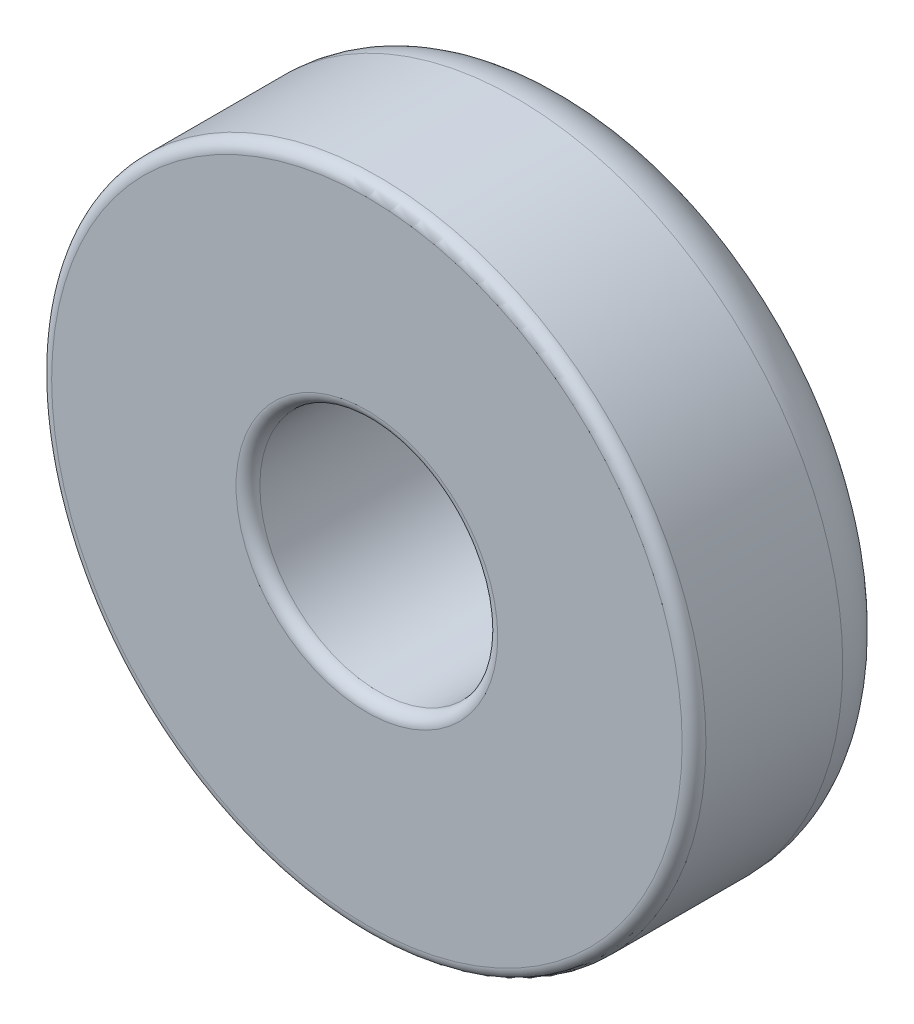
SolidWorks part; units mm, degrees
material "iglidur® X"
ref_plane "Front Plane" through (0, 0, 0) normal (0, 0, 1) x (1, 0, 0)
ref_plane "Top Plane" through (0, 0, 0) normal (0, 1, 0) x (1, 0, 0)
ref_plane "Right Plane" through (0, 0, 0) normal (1, 0, 0) x (0, 0, -1)
sketch "Sketch1" plane through (0, 0, 0) normal (0, 0, 1) x (1, 0, 0)
  circle A0 centre (0, 0) radius 1
  dimension "D1" = 2
extrude "Extrude-Thin1" add sketch "Sketch1" along normal blind 1.75 thin
fillet "Fillet1" radius 0.5 1 edges at (2.75, 0, 0)
fillet "Fillet2" radius 0.1 3 edges at (1, 0, 0) (1, 0, 1.75) (2.75, 0, 1.75)
